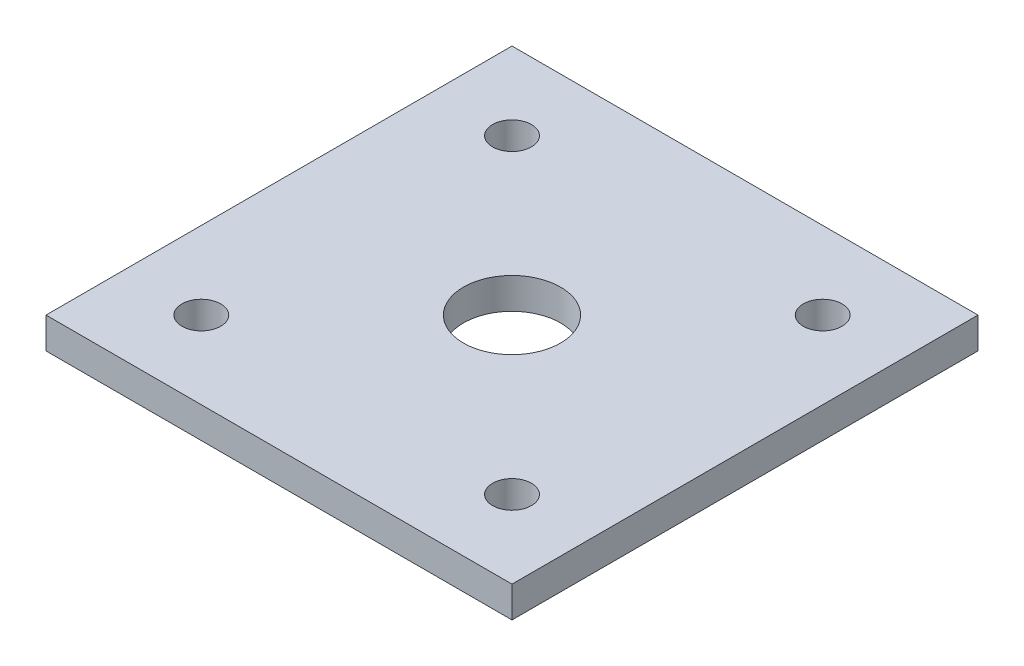
SolidWorks part; units mm, degrees
ref_plane "Front Plane" through (0, 0, 0) normal (0, 0, 1) x (1, 0, 0)
ref_plane "Top Plane" through (0, 0, 0) normal (0, 1, 0) x (1, 0, 0)
ref_plane "Right Plane" through (0, 0, 0) normal (1, 0, 0) x (0, 0, -1)
sketch "Sketch3" plane through (0, 0, 0) normal (0, 1, 0) x (1, 0, 0)
  line L1 (60, -60) -> (-60, -60)
  line L2 (60, -60) -> (60, 60)
  line L3 (60, 60) -> (-60, 60)
  line L4 (-60, -60) -> (-60, 60)
  line L5 (60, -60) -> (-60, 60) construction
  line L6 (60, 60) -> (-60, -60) construction
  point P0 (0, 0)
  dimension "D1" = 120
extrude "Boss-Extrude2" add sketch "Sketch3" along normal blind 8
sketch "Sketch5" plane through (0, 8, 0) normal (0, 1, 0) x (1, 0, 0)
  circle A0 centre (0, 0) radius 12.5
  dimension "D1" = 25
extrude "Cut-Extrude1" cut sketch "Sketch5" against normal through all
sketch "Sketch6" plane through (0, 8, 0) normal (0, 1, 0) x (1, 0, 0)
  line L0 (-60, 60) -> (-60, -60) construction
  line L1 (60, 60) -> (-60, 60) construction
  circle A0 centre (-40, 40) radius 5
  dimension "D1" = 10
  dimension "D3" = 20
  dimension "D2" = 20
extrude "Cut-Extrude2" cut sketch "Sketch6" against normal through all
pattern_linear "LPattern1" count 2 spacing 80 along (0, 0, 1) count 2 spacing 80 along (1, 0, 0) of "Cut-Extrude2"
